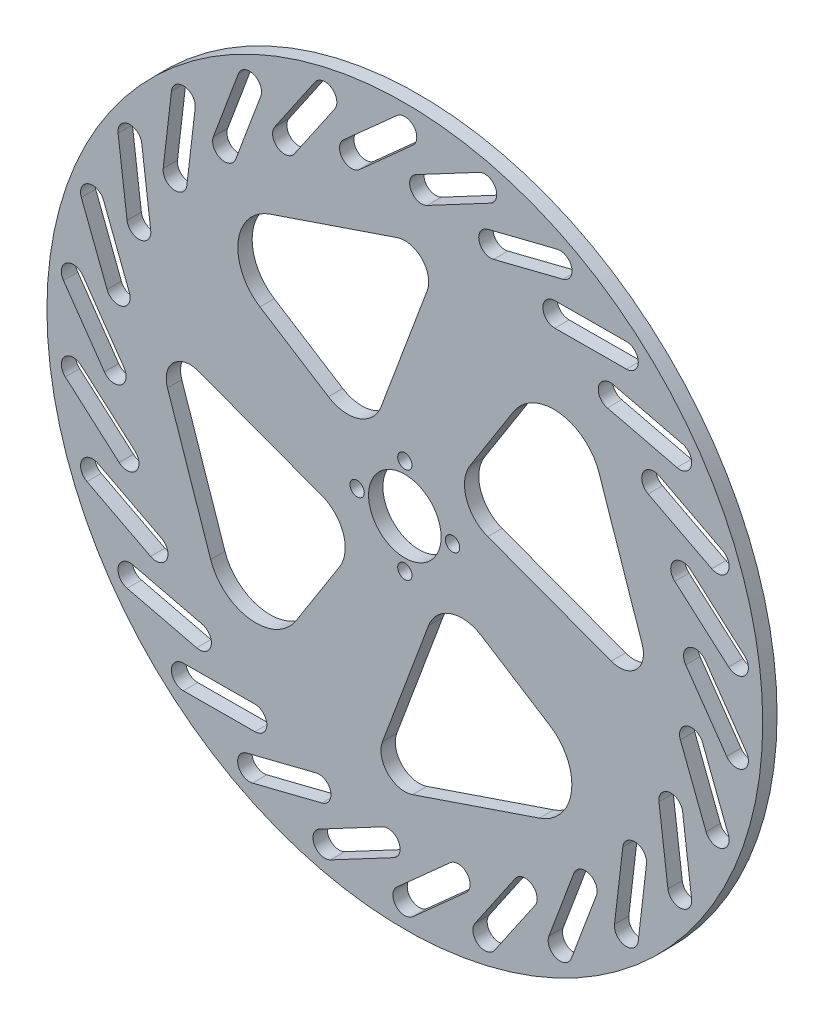
SolidWorks part; units mm, degrees
material "A286 Iron Base Superalloy"
ref_plane "Front Plane" through (0, 0, 0) normal (0, 0, 1) x (1, 0, 0)
ref_plane "Top Plane" through (0, 0, 0) normal (0, 1, 0) x (1, 0, 0)
ref_plane "Right Plane" through (0, 0, 0) normal (1, 0, 0) x (0, 0, -1)
sketch "Sketch1" plane through (0, 0, 0) normal (0, 0, 1) x (1, 0, 0)
  line L0 (0, 0) -> (0, 30.7018) construction
  line L1 (-4.9735, 17.3773) -> (4.6843, 43.2515)
  line L2 (-30.3641, 22.7854) -> (-16.0231, 13.6703)
  line L3 (-28.2171, 40.6934) -> (-1.6085, 49.7342)
  line L4 (0, 50) -> (0, 75) construction
  line L5 (22.7854, 30.3641) -> (13.6703, 16.0231)
  line L6 (17.3773, 4.9735) -> (43.2515, -4.6843)
  line L7 (40.6934, 28.2171) -> (49.7342, 1.6085)
  line L8 (30.3641, -22.7854) -> (16.0231, -13.6703)
  line L9 (4.9735, -17.3773) -> (-4.6843, -43.2515)
  line L10 (28.2171, -40.6934) -> (1.6085, -49.7342)
  line L11 (-22.7854, -30.3641) -> (-13.6703, -16.0231)
  line L12 (-17.3773, -4.9735) -> (-43.2515, 4.6843)
  line L13 (-40.6934, -28.2171) -> (-49.7342, -1.6085)
  line L14 (0, 70) -> (-11.1803, 60) construction
  line L15 (1.6667, 68.1366) -> (-9.5137, 58.1366)
  line L16 (-1.6667, 71.8634) -> (-12.847, 61.8634)
  line L17 (16.7521, 67.9659) -> (3.5035, 60.9321) construction
  line L18 (17.9244, 65.7578) -> (4.6758, 58.724)
  line L19 (15.5798, 70.174) -> (2.3312, 63.1402)
  line L20 (32.5306, 61.9819) -> (17.9837, 58.3231) construction
  line L21 (33.1404, 59.5574) -> (18.5935, 55.8986)
  line L22 (31.9208, 64.4064) -> (17.3739, 60.7476)
  line L23 (46.4186, 52.3958) -> (31.4188, 52.3246) construction
  line L24 (46.4304, 49.8958) -> (31.4306, 49.8246)
  line L25 (46.4067, 54.8957) -> (31.4069, 54.8246)
  line L26 (57.6089, 39.7645) -> (43.0279, 43.2851) construction
  line L27 (57.0221, 37.3344) -> (42.4411, 40.855)
  line L28 (58.1956, 42.1947) -> (43.6146, 45.7153)
  line L29 (65.4511, 24.8223) -> (52.1364, 31.7301) construction
  line L30 (64.2998, 22.6032) -> (50.9851, 29.511)
  line L31 (66.6024, 27.0415) -> (53.2877, 33.9492)
  line L32 (69.4896, 8.4376) -> (58.2149, 18.331) construction
  line L33 (67.8407, 6.5584) -> (56.566, 16.4519)
  line L34 (71.1385, 10.3167) -> (59.8638, 20.2101)
  line L35 (69.4896, -8.4376) -> (60.9102, 3.8666) construction
  line L36 (67.4389, -9.8675) -> (58.8595, 2.4367)
  line L37 (71.5403, -7.0077) -> (62.9609, 5.2965)
  line L38 (65.4511, -24.8223) -> (60.0656, -10.8225) construction
  line L39 (63.1178, -25.7199) -> (57.7323, -11.7201)
  line L40 (67.7844, -23.9247) -> (62.3989, -9.9249)
  line L41 (57.6089, -39.7645) -> (55.7302, -24.8826) construction
  line L42 (55.1286, -40.0776) -> (53.2499, -25.1958)
  line L43 (60.0892, -39.4514) -> (58.2105, -24.5695)
  line L44 (46.4186, -52.3958) -> (48.156, -37.4967) construction
  line L45 (43.9354, -52.1062) -> (45.6728, -37.2071)
  line L46 (48.9018, -52.6853) -> (50.6391, -37.7863)
  line L47 (32.5306, -61.9819) -> (37.7831, -47.9316) construction
  line L48 (30.1889, -61.1065) -> (35.4414, -47.0562)
  line L49 (34.8723, -62.8573) -> (40.1248, -48.807)
  line L50 (16.7521, -67.9659) -> (25.2144, -55.5809) construction
  line L51 (14.6879, -66.5555) -> (23.1502, -54.1705)
  line L52 (18.8163, -69.3763) -> (27.2786, -56.9913)
  line L53 (0, -70) -> (11.1803, -60) construction
  line L54 (-1.6667, -68.1366) -> (9.5137, -58.1366)
  line L55 (1.6667, -71.8634) -> (12.847, -61.8634)
  line L56 (-16.7521, -67.9659) -> (-3.5035, -60.9321) construction
  line L57 (-17.9244, -65.7578) -> (-4.6758, -58.724)
  line L58 (-15.5798, -70.174) -> (-2.3312, -63.1402)
  line L59 (-32.5306, -61.9819) -> (-17.9837, -58.3231) construction
  line L60 (-33.1404, -59.5574) -> (-18.5935, -55.8986)
  line L61 (-31.9208, -64.4064) -> (-17.3739, -60.7476)
  line L62 (-46.4186, -52.3958) -> (-31.4188, -52.3246) construction
  line L63 (-46.4304, -49.8958) -> (-31.4306, -49.8246)
  line L64 (-46.4067, -54.8957) -> (-31.4069, -54.8246)
  line L65 (-57.6089, -39.7645) -> (-43.0279, -43.2851) construction
  line L66 (-57.0221, -37.3344) -> (-42.4411, -40.855)
  line L67 (-58.1956, -42.1947) -> (-43.6146, -45.7153)
  line L68 (-65.4511, -24.8223) -> (-52.1364, -31.7301) construction
  line L69 (-64.2998, -22.6032) -> (-50.9851, -29.511)
  line L70 (-66.6024, -27.0415) -> (-53.2877, -33.9492)
  line L71 (-69.4896, -8.4376) -> (-58.2149, -18.331) construction
  line L72 (-67.8407, -6.5584) -> (-56.566, -16.4519)
  line L73 (-71.1385, -10.3167) -> (-59.8638, -20.2101)
  line L74 (-69.4896, 8.4376) -> (-60.9102, -3.8666) construction
  line L75 (-67.4389, 9.8675) -> (-58.8595, -2.4367)
  line L76 (-71.5403, 7.0077) -> (-62.9609, -5.2965)
  line L77 (-65.4511, 24.8223) -> (-60.0656, 10.8225) construction
  line L78 (-63.1178, 25.7199) -> (-57.7323, 11.7201)
  line L79 (-67.7844, 23.9247) -> (-62.3989, 9.9249)
  line L80 (-57.6089, 39.7645) -> (-55.7302, 24.8826) construction
  line L81 (-55.1286, 40.0776) -> (-53.2499, 25.1958)
  line L82 (-60.0892, 39.4514) -> (-58.2105, 24.5695)
  line L83 (-46.4186, 52.3958) -> (-48.156, 37.4967) construction
  line L84 (-43.9354, 52.1062) -> (-45.6728, 37.2071)
  line L85 (-48.9018, 52.6853) -> (-50.6391, 37.7863)
  line L86 (-32.5306, 61.9819) -> (-37.7831, 47.9316) construction
  line L87 (-30.1889, 61.1065) -> (-35.4414, 47.0562)
  line L88 (-34.8723, 62.8573) -> (-40.1248, 48.807)
  line L89 (-16.7521, 67.9659) -> (-25.2144, 55.5809) construction
  line L90 (-14.6879, 66.5555) -> (-23.1502, 54.1705)
  line L91 (-18.8163, 69.3763) -> (-27.2786, 56.9913)
  circle A0 centre (0, 0) radius 75
  circle A1 centre (0, 0) radius 55 construction
  circle A2 centre (0, 0) radius 50 construction
  circle A3 centre (0, 0) radius 7.6
  arc A4 (-28.2171, 40.6934) -> (-30.3641, 22.7854) centre (-25, 31.225) ccw
  arc A5 (-16.0231, 13.6703) -> (-4.9735, 17.3773) centre (-12, 20) ccw
  arc A6 (4.6843, 43.2515) -> (-1.6085, 49.7342) centre (0, 45) ccw
  circle A7 centre (0, 0) radius 55 construction
  arc A8 (40.6934, 28.2171) -> (22.7854, 30.3641) centre (31.225, 25) ccw
  arc A9 (13.6703, 16.0231) -> (17.3773, 4.9735) centre (20, 12) ccw
  arc A10 (43.2515, -4.6843) -> (49.7342, 1.6085) centre (45, 0) ccw
  circle A11 centre (0, 0) radius 55 construction
  arc A12 (28.2171, -40.6934) -> (30.3641, -22.7854) centre (25, -31.225) ccw
  arc A13 (16.0231, -13.6703) -> (4.9735, -17.3773) centre (12, -20) ccw
  arc A14 (-4.6843, -43.2515) -> (1.6085, -49.7342) centre (0, -45) ccw
  circle A15 centre (0, 0) radius 55 construction
  arc A16 (-40.6934, -28.2171) -> (-22.7854, -30.3641) centre (-31.225, -25) ccw
  arc A17 (-13.6703, -16.0231) -> (-17.3773, -4.9735) centre (-20, -12) ccw
  arc A18 (-43.2515, 4.6843) -> (-49.7342, -1.6085) centre (-45, 0) ccw
  arc A19 (1.6667, 68.1366) -> (-1.6667, 71.8634) centre (0, 70) ccw
  arc A20 (-12.847, 61.8634) -> (-9.5137, 58.1366) centre (-11.1803, 60) ccw
  circle A21 centre (0, 0) radius 50 construction
  arc A22 (17.9244, 65.7578) -> (15.5798, 70.174) centre (16.7521, 67.9659) ccw
  arc A23 (2.3312, 63.1402) -> (4.6758, 58.724) centre (3.5035, 60.9321) ccw
  circle A24 centre (0, 0) radius 50 construction
  arc A25 (33.1404, 59.5574) -> (31.9208, 64.4064) centre (32.5306, 61.9819) ccw
  arc A26 (17.3739, 60.7476) -> (18.5935, 55.8986) centre (17.9837, 58.3231) ccw
  circle A27 centre (0, 0) radius 50 construction
  arc A28 (46.4304, 49.8958) -> (46.4067, 54.8957) centre (46.4186, 52.3958) ccw
  arc A29 (31.4069, 54.8246) -> (31.4306, 49.8246) centre (31.4188, 52.3246) ccw
  circle A30 centre (0, 0) radius 50 construction
  arc A31 (57.0221, 37.3344) -> (58.1956, 42.1947) centre (57.6089, 39.7645) ccw
  arc A32 (43.6146, 45.7153) -> (42.4411, 40.855) centre (43.0279, 43.2851) ccw
  circle A33 centre (0, 0) radius 50 construction
  arc A34 (64.2998, 22.6032) -> (66.6024, 27.0415) centre (65.4511, 24.8223) ccw
  arc A35 (53.2877, 33.9492) -> (50.9851, 29.511) centre (52.1364, 31.7301) ccw
  circle A36 centre (0, 0) radius 50 construction
  arc A37 (67.8407, 6.5584) -> (71.1385, 10.3167) centre (69.4896, 8.4376) ccw
  arc A38 (59.8638, 20.2101) -> (56.566, 16.4519) centre (58.2149, 18.331) ccw
  circle A39 centre (0, 0) radius 50 construction
  arc A40 (67.4389, -9.8675) -> (71.5403, -7.0077) centre (69.4896, -8.4376) ccw
  arc A41 (62.9609, 5.2965) -> (58.8595, 2.4367) centre (60.9102, 3.8666) ccw
  circle A42 centre (0, 0) radius 50 construction
  arc A43 (63.1178, -25.7199) -> (67.7844, -23.9247) centre (65.4511, -24.8223) ccw
  arc A44 (62.3989, -9.9249) -> (57.7323, -11.7201) centre (60.0656, -10.8225) ccw
  circle A45 centre (0, 0) radius 50 construction
  arc A46 (55.1286, -40.0776) -> (60.0892, -39.4514) centre (57.6089, -39.7645) ccw
  arc A47 (58.2105, -24.5695) -> (53.2499, -25.1958) centre (55.7302, -24.8826) ccw
  circle A48 centre (0, 0) radius 50 construction
  arc A49 (43.9354, -52.1062) -> (48.9018, -52.6853) centre (46.4186, -52.3958) ccw
  arc A50 (50.6391, -37.7863) -> (45.6728, -37.2071) centre (48.156, -37.4967) ccw
  circle A51 centre (0, 0) radius 50 construction
  arc A52 (30.1889, -61.1065) -> (34.8723, -62.8573) centre (32.5306, -61.9819) ccw
  arc A53 (40.1248, -48.807) -> (35.4414, -47.0562) centre (37.7831, -47.9316) ccw
  circle A54 centre (0, 0) radius 50 construction
  arc A55 (14.6879, -66.5555) -> (18.8163, -69.3763) centre (16.7521, -67.9659) ccw
  arc A56 (27.2786, -56.9913) -> (23.1502, -54.1705) centre (25.2144, -55.5809) ccw
  circle A57 centre (0, 0) radius 50 construction
  arc A58 (-1.6667, -68.1366) -> (1.6667, -71.8634) centre (0, -70) ccw
  arc A59 (12.847, -61.8634) -> (9.5137, -58.1366) centre (11.1803, -60) ccw
  circle A60 centre (0, 0) radius 50 construction
  arc A61 (-17.9244, -65.7578) -> (-15.5798, -70.174) centre (-16.7521, -67.9659) ccw
  arc A62 (-2.3312, -63.1402) -> (-4.6758, -58.724) centre (-3.5035, -60.9321) ccw
  circle A63 centre (0, 0) radius 50 construction
  arc A64 (-33.1404, -59.5574) -> (-31.9208, -64.4064) centre (-32.5306, -61.9819) ccw
  arc A65 (-17.3739, -60.7476) -> (-18.5935, -55.8986) centre (-17.9837, -58.3231) ccw
  circle A66 centre (0, 0) radius 50 construction
  arc A67 (-46.4304, -49.8958) -> (-46.4067, -54.8957) centre (-46.4186, -52.3958) ccw
  arc A68 (-31.4069, -54.8246) -> (-31.4306, -49.8246) centre (-31.4188, -52.3246) ccw
  circle A69 centre (0, 0) radius 50 construction
  arc A70 (-57.0221, -37.3344) -> (-58.1956, -42.1947) centre (-57.6089, -39.7645) ccw
  arc A71 (-43.6146, -45.7153) -> (-42.4411, -40.855) centre (-43.0279, -43.2851) ccw
  circle A72 centre (0, 0) radius 50 construction
  arc A73 (-64.2998, -22.6032) -> (-66.6024, -27.0415) centre (-65.4511, -24.8223) ccw
  arc A74 (-53.2877, -33.9492) -> (-50.9851, -29.511) centre (-52.1364, -31.7301) ccw
  circle A75 centre (0, 0) radius 50 construction
  arc A76 (-67.8407, -6.5584) -> (-71.1385, -10.3167) centre (-69.4896, -8.4376) ccw
  arc A77 (-59.8638, -20.2101) -> (-56.566, -16.4519) centre (-58.2149, -18.331) ccw
  circle A78 centre (0, 0) radius 50 construction
  arc A79 (-67.4389, 9.8675) -> (-71.5403, 7.0077) centre (-69.4896, 8.4376) ccw
  arc A80 (-62.9609, -5.2965) -> (-58.8595, -2.4367) centre (-60.9102, -3.8666) ccw
  circle A81 centre (0, 0) radius 50 construction
  arc A82 (-63.1178, 25.7199) -> (-67.7844, 23.9247) centre (-65.4511, 24.8223) ccw
  arc A83 (-62.3989, 9.9249) -> (-57.7323, 11.7201) centre (-60.0656, 10.8225) ccw
  circle A84 centre (0, 0) radius 50 construction
  arc A85 (-55.1286, 40.0776) -> (-60.0892, 39.4514) centre (-57.6089, 39.7645) ccw
  arc A86 (-58.2105, 24.5695) -> (-53.2499, 25.1958) centre (-55.7302, 24.8826) ccw
  circle A87 centre (0, 0) radius 50 construction
  arc A88 (-43.9354, 52.1062) -> (-48.9018, 52.6853) centre (-46.4186, 52.3958) ccw
  arc A89 (-50.6391, 37.7863) -> (-45.6728, 37.2071) centre (-48.156, 37.4967) ccw
  circle A90 centre (0, 0) radius 50 construction
  arc A91 (-30.1889, 61.1065) -> (-34.8723, 62.8573) centre (-32.5306, 61.9819) ccw
  arc A92 (-40.1248, 48.807) -> (-35.4414, 47.0562) centre (-37.7831, 47.9316) ccw
  circle A93 centre (0, 0) radius 50 construction
  arc A94 (-14.6879, 66.5555) -> (-18.8163, 69.3763) centre (-16.7521, 67.9659) ccw
  arc A95 (-27.2786, 56.9913) -> (-23.1502, 54.1705) centre (-25.2144, 55.5809) ccw
  circle A96 centre (0, 10) radius 1.5
  circle A97 centre (0, 0) radius 55 construction
  circle A98 centre (10, 0) radius 1.5
  circle A99 centre (0, 0) radius 55 construction
  circle A100 centre (0, -10) radius 1.5
  circle A101 centre (0, 0) radius 55 construction
  circle A102 centre (-10, 0) radius 1.5
  point P20 (-5.5902, 65)
  point P51 (0, 0)
  point P62 (10.1278, 64.449)
  point P70 (25.2572, 60.1525)
  point P78 (38.9187, 52.3602)
  point P86 (50.3184, 41.5248)
  point P94 (58.7938, 28.2762)
  point P102 (63.8523, 13.3843)
  point P110 (65.1999, -2.2855)
  point P118 (62.7584, -17.8224)
  point P126 (56.6695, -32.3236)
  point P134 (47.2873, -44.9462)
  point P142 (35.1569, -54.9568)
  point P150 (20.9832, -61.7734)
  point P158 (5.5902, -65)
  point P166 (-10.1278, -64.449)
  point P174 (-25.2572, -60.1525)
  point P182 (-38.9187, -52.3602)
  point P190 (-50.3184, -41.5248)
  point P198 (-58.7938, -28.2762)
  point P206 (-63.8523, -13.3843)
  point P214 (-65.1999, 2.2855)
  point P222 (-62.7584, 17.8224)
  point P230 (-56.6695, 32.3236)
  point P238 (-47.2873, 44.9462)
  point P246 (-35.1569, 54.9568)
  point P254 (-20.9832, 61.7734)
  point P259 (0, 0)
  point P271 (0, 0)
  dimension "D1" = 150
  dimension "D2" = 110
  dimension "D3" = 100
  dimension "D4" = 15.2
  dimension "D5" = 10
  dimension "D6" = 15
  dimension "D7" = 20
  dimension "D8" = 25
  dimension "D11" = 28.5438
  dimension "D12" = 4
  dimension "D14" = 2.5
  dimension "D18" = 3
  dimension "D9" = 12
  dimension "D10" = 20
  dimension "D13" = 15
  dimension "D15" = 5
  dimension "D16" = 60
  dimension "D19" = 10
  dimension "D17" = 26
  dimension "D20" = 4
extrude "Boss-Extrude1" add sketch "Sketch1" along normal blind 3
